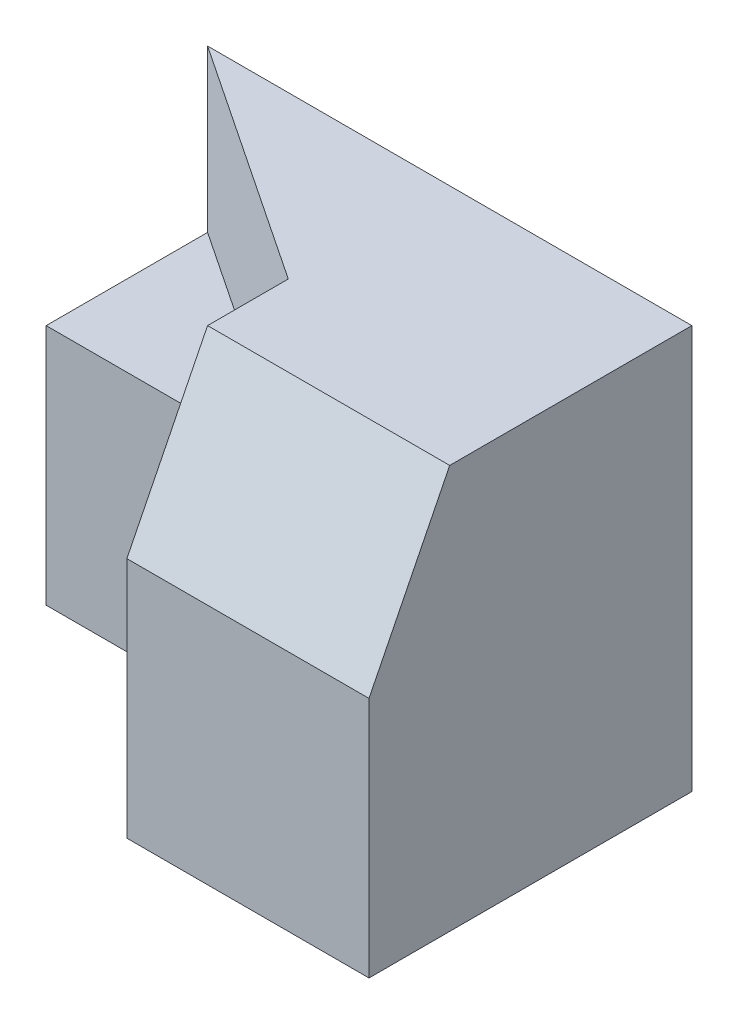
SolidWorks part; units mm, degrees
ref_plane "Front Plane" through (0, 0, 0) normal (0, 0, 1) x (1, 0, 0)
ref_plane "Top Plane" through (0, 0, 0) normal (0, 1, 0) x (1, 0, 0)
ref_plane "Right Plane" through (0, 0, 0) normal (1, 0, 0) x (0, 0, -1)
sketch "Sketch1" plane through (0, 0, 0) normal (0, 0, 1) x (1, 0, 0)
  line L1 (0, 0) -> (30, 0)
  line L2 (0, 0) -> (0, 25)
  line L3 (0, 25) -> (30, 25)
  line L4 (30, 0) -> (30, 25)
  dimension "D1" = 30
  dimension "D2" = 25
extrude "Boss-Extrude1" add sketch "Sketch1" along normal blind 20
sketch "Sketch2" plane through (0, 0, 20) normal (0, 0, 1) x (1, 0, 0)
  line L0 (30, 25) -> (0, 25) construction
  line L1 (0, 0) -> (15, 0)
  line L2 (0, 0) -> (0, 25)
  line L3 (0, 25) -> (15, 25)
  line L4 (15, 0) -> (15, 25)
extrude "Cut-Extrude1" cut sketch "Sketch2" against normal blind 10
sketch "Sketch3" plane through (15, 0, 0) normal (-1, 0, 0) x (0, 0, 1)
  line L0 (15, 25) -> (20, 15)
  line L1 (10, 25) -> (20, 25) construction
  line L2 (20, 0) -> (20, 25) construction
  line L3 (20, 15) -> (20, 25)
  line L4 (20, 25) -> (15, 25)
  dimension "D1" = 10
  dimension "D2" = 5
extrude "Cut-Extrude2" cut sketch "Sketch3" against normal blind 20
sketch "Sketch4" plane through (0, 25, 0) normal (0, 1, 0) x (1, 0, 0)
  line L0 (15, -10) -> (0, 0)
  line L1 (0, 0) -> (0, -10)
  line L2 (0, -10) -> (15, -10)
extrude "Cut-Extrude3" cut sketch "Sketch4" against normal blind 10
